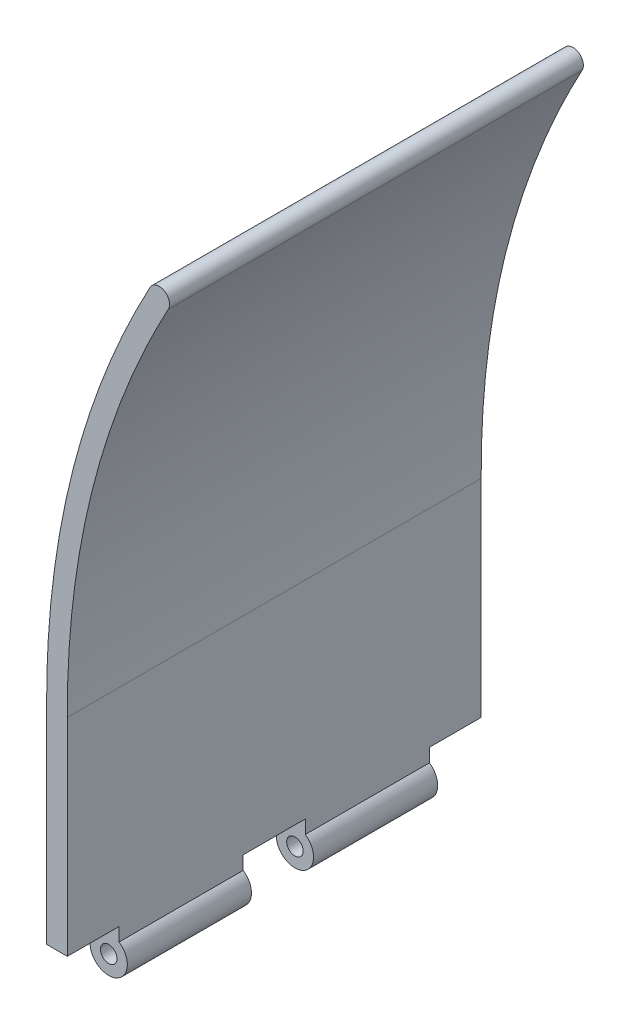
SolidWorks part; units mm, degrees
ref_plane "Front Plane" through (0, 0, 0) normal (0, 0, 1) x (1, 0, 0)
ref_plane "Top Plane" through (0, 0, 0) normal (0, 1, 0) x (1, 0, 0)
ref_plane "Right Plane" through (0, 0, 0) normal (1, 0, 0) x (0, 0, -1)
sketch "Sketch1" plane through (0, 0, 0) normal (0, 0, 1) x (1, 0, 0)
  line L0 (0, 0) -> (0, 50)
  line L1 (5, 0) -> (5, 50.0111)
  line L2 (1.4385, 50) -> (50001.4385, 50) construction
  line L3 (-50.7533, 150) -> (98.0256, 150) construction
  line L4 (0, 40.0501) -> (0, 50040.0501) construction
  line L5 (25, 0) -> (25, 50000) construction
  line L6 (0, 0) -> (5, 0)
  line L7 (25, 150) -> (44013.0948, -23620.7281) construction
  arc A0 (29.3988, 147.6229) -> (25, 150) centre (27.1994, 148.8115) ccw
  spline S0 degree 2 poles (0, 50) (-0.2361, 103.3002) (25, 150) knots 0 0 0 1 1 1
  spline S1 degree 1 poles (5, 50.0111) (29.3988, 147.6229) knots 0 0 1 1 construction
  spline S2 degree 3 poles (5, 50.0111) (4.9904, 52.1737) (5.0356, 56.5116) (5.3858, 65.0832) (6.3088, 75.676) (8.1926, 88.1732) (10.852, 100.466) (14.2879, 112.5571) (18.5007, 124.4492) (22.6626, 134.2004) (26.3791, 141.8981) (28.375, 145.7283) (29.3988, 147.6229) knots -0.000104 -0.000104 -0.000104 -0.000104 0.062403 0.124909 0.249922 0.374935 0.499948 0.624961 0.749974 0.874987 0.937494 1 1 1 1
  point P18 (0, 0)
  dimension "D1" = 50
  dimension "D2" = 100
  dimension "D3" = 25
  dimension "D4" = 7
  dimension "D5" = 55
  dimension "D6" = 5
extrude "Boss-Extrude1" add sketch "Sketch1" along normal mid plane 100
sketch "Sketch2" plane through (0, 0, 50) normal (0, 0, 1) x (1, 0, 0)
  line L0 (0, 0) -> (5, 0) construction
  line L1 (0, 0) -> (0, -3.2583)
  line L2 (0, -3.2583) -> (5, -3.2583)
  line L3 (5, -3.2583) -> (5, 0)
  line L4 (5, 0) -> (0, 0)
  circle A1 centre (2.5, -7) radius 4.5
  circle A2 centre (2.5, -7) radius 2
  point P7 (2.5, 0)
  line M2 (0, 0) -> (5, 0)
  dimension "D1" = 9
  dimension "D2" = 4
  dimension "D3" = 7
extrude "Boss-Extrude2" add sketch "Sketch2" against normal blind 30 from offset 12.5 contours L2 A1 A2 | L2 A1 | A1 L3 L1 M2 offset against normal yes
mirror "Mirror1" about plane through (0, 0, 0) normal (0, 0, 1) of "Boss-Extrude2"
